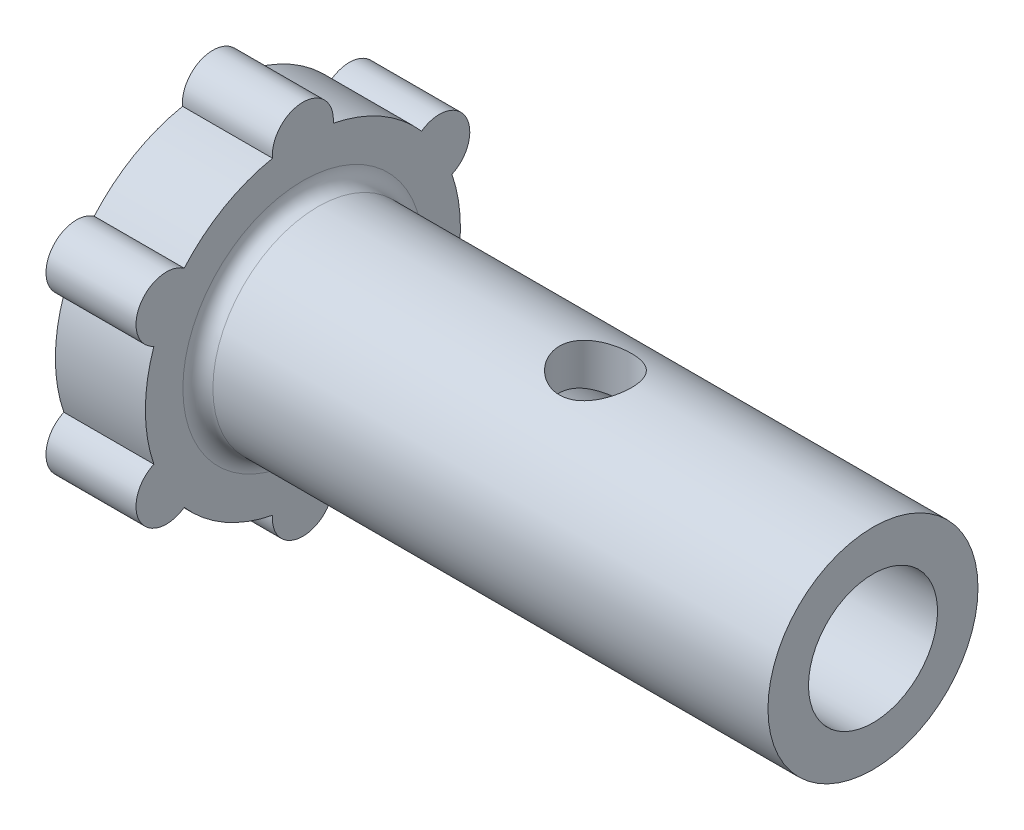
SolidWorks part; units mm, degrees
ref_plane "Front Plane" through (0, 0, 0) normal (0, 0, 1) x (1, 0, 0)
ref_plane "Top Plane" through (0, 0, 0) normal (0, 1, 0) x (1, 0, 0)
ref_plane "Right Plane" through (0, 0, 0) normal (1, 0, 0) x (0, 0, -1)
sketch "Sketch1" plane through (0, 0, 0) normal (0, 0, 1) x (1, 0, 0)
  line L0 (-11, 0) -> (11, 0) construction
  line L1 (11, 2.15) -> (11, 3.5)
  line L2 (11, 3.5) -> (-8, 3.5)
  line L3 (-8, 3.5) -> (-8, 5.25)
  line L4 (-8, 5.25) -> (-11, 5.25)
  line L5 (-11, 5.25) -> (-11, 3.5)
  line L6 (-9.524, 2.15) -> (11, 2.15)
  line L7 (-11, 3.5) -> (-11, 0) construction
  line L8 (11, 0) -> (11, 2.15) construction
  line L9 (-11, 3.5) -> (-9.524, 3.5)
  line L10 (-9.524, 3.5) -> (-9.524, 2.15)
  dimension "D1" = 2.15
  dimension "D2" = 19
  dimension "D3" = 7
  dimension "D4" = 3
  dimension "D5" = 1.524
  dimension "D6" = 3.5
  dimension "D7" = 10.5
revolve "Revolve1" add sketch "Sketch1" angle 360 about L0
fillet "Fillet1" radius 0.5 1 edges at (-8, 0, 3.5)
fillet "Fillet2" radius 0.2 1 edges at (-9.524, 0, 3.5)
sketch "Sketch2" plane through (0, 0, 0) normal (0, 1, 0) x (1, 0, 0)
  line L0 (-7.5, 0) -> (11, 0) construction
  line L1 (-7.5, -3.5) -> (-7.5, 3.5) construction
  line L2 (11, -3.5) -> (11, 3.5) construction
  circle A0 centre (1.75, 0) radius 1.2
  dimension "D1" = 2.4
extrude "Cut-Extrude1" cut sketch "Sketch2" against normal through all and the other way through all
sketch "Sketch3" plane through (-11, 0, 0) normal (-1, 0, 0) x (0, 0, 1)
  line L0 (0, 5.25) -> (0, -5.25) construction
  line L1 (5.25, 0) -> (-5.25, 0) construction
  circle A0 centre (0, 0) radius 5.25 construction
  circle A1 centre (0, 0) radius 5.25 construction
  arc A2 (1.0112, 5.1517) -> (-1.0112, 5.1517) centre (0, 5.25) ccw
  arc A3 (-1.0112, 5.1517) -> (1.0112, 5.1517) centre (0, 0) cw
  circle A4 centre (0, 0) radius 5.25 construction
  arc A5 (4.9671, 1.7001) -> (3.9559, 3.4516) centre (4.5466, 2.625) ccw
  arc A6 (3.9559, 3.4516) -> (4.9671, 1.7001) centre (0, 0) cw
  circle A7 centre (0, 0) radius 5.25 construction
  arc A8 (3.9559, -3.4516) -> (4.9671, -1.7001) centre (4.5466, -2.625) ccw
  arc A9 (4.9671, -1.7001) -> (3.9559, -3.4516) centre (0, 0) cw
  circle A10 centre (0, 0) radius 5.25 construction
  arc A11 (-1.0112, -5.1517) -> (1.0112, -5.1517) centre (0, -5.25) ccw
  arc A12 (1.0112, -5.1517) -> (-1.0112, -5.1517) centre (0, 0) cw
  circle A13 centre (0, 0) radius 5.25 construction
  arc A14 (-4.9671, -1.7001) -> (-3.9559, -3.4516) centre (-4.5466, -2.625) ccw
  arc A15 (-3.9559, -3.4516) -> (-4.9671, -1.7001) centre (0, 0) cw
  circle A16 centre (0, 0) radius 5.25 construction
  arc A17 (-3.9559, 3.4516) -> (-4.9671, 1.7001) centre (-4.5466, 2.625) ccw
  arc A18 (-4.9671, 1.7001) -> (-3.9559, 3.4516) centre (0, 0) cw
  point P11 (0, 0)
  point P35 (0, 0)
  dimension "D1" = 1.016
  dimension "D2" = 6
extrude "Boss-Extrude1" add sketch "Sketch3" against normal up to surface (3 mm away) up to face at (-8, 0, 4)
